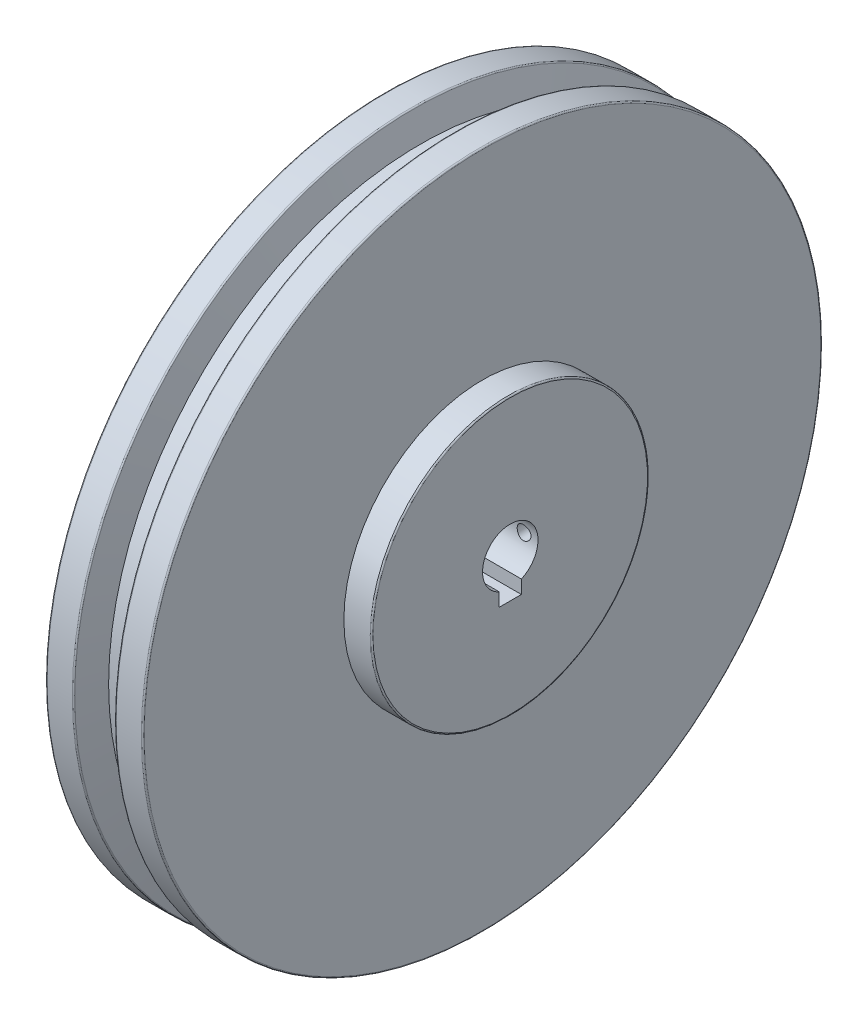
SolidWorks part; units mm, degrees
ref_plane "Front Plane" through (0, 0, 0) normal (0, 0, 1) x (1, 0, 0)
ref_plane "Top Plane" through (0, 0, 0) normal (0, 1, 0) x (1, 0, 0)
ref_plane "Right Plane" through (0, 0, 0) normal (1, 0, 0) x (0, 0, -1)
sketch "Sketch1" plane through (0, 0, 0) normal (0, 0, 1) x (1, 0, 0)
  line L0 (0, 0) -> (43.9763, 0) construction
  line L1 (0, -20) -> (0, -122)
  line L2 (0.5, -122.5) -> (9.6163, -122.5)
  line L3 (10.0993, -122.1294) -> (12.6795, -112.5)
  line L4 (12.6795, -112.5) -> (22.3205, -112.5)
  line L5 (22.3205, -112.5) -> (24.9007, -122.1294)
  line L6 (25.3837, -122.5) -> (34.5, -122.5)
  line L7 (35, -122) -> (35, -50)
  line L8 (35, -50) -> (44.5, -50)
  line L9 (45, -49.5) -> (45, -10)
  line L10 (45, -10) -> (2.5, -10)
  line L11 (0, -20) -> (2.5, -10)
  arc A0 (44.5, -50) -> (45, -49.5) centre (44.5, -49.5) ccw
  arc A1 (34.5, -122.5) -> (35, -122) centre (34.5, -122) ccw
  arc A2 (24.9007, -122.1294) -> (25.3837, -122.5) centre (25.3837, -122) ccw
  arc A3 (9.6163, -122.5) -> (10.0993, -122.1294) centre (9.6163, -122) ccw
  arc A4 (0, -122) -> (0.5, -122.5) centre (0.5, -122) ccw
  point P18 (35, -122.5)
  point P21 (25, -122.5)
  point P24 (10, -122.5)
  point P27 (0, -122.5)
  dimension "D14" = 100
  dimension "D15" = 0.5
  dimension "D10" = 0.5
  dimension "D1" = 20
  dimension "D2" = 245
  dimension "D3" = 225
  dimension "D4" = 245
  dimension "D5" = 105
  dimension "D6" = 10
  dimension "D7" = 10
  dimension "D8" = 15
  dimension "D9" = 105
  dimension "D11" = 45
  dimension "D12" = 2.5
  dimension "D13" = 10
revolve "Revolve1" add sketch "Sketch1" angle 360 about L0
sketch "Esboço1" plane through (0, 0, 0) normal (-1, 0, 0) x (0, 0, 1)
  line L0 (0, 0) -> (0, -10) construction
  line L1 (4, -14) -> (-4, -14)
  line L2 (4, -14) -> (4, -6)
  line L3 (4, -6) -> (-4, -6)
  line L4 (-4, -14) -> (-4, -6)
  line L5 (4, -14) -> (-4, -6) construction
  line L6 (4, -6) -> (-4, -14) construction
  circle A0 centre (0, 0) radius 10 construction
  point P0 (0, -10)
  dimension "D1" = 8
  dimension "D2" = 8
extrude "Corte-extrusão1" cut sketch "Esboço1" against normal through all
sketch "Esboço3" plane through (0, 0, 0) normal (0, 0, 1) x (1, 0, 0)
  line L0 (45, 0) -> (35, 0) construction
  line L1 (45, -49.5) -> (45, 49.5) construction
  line L2 (35, -50) -> (35, 50) construction
  circle A0 centre (40, 0) radius 2.5
  dimension "D1" = 5
extrude "Corte-extrusão2" cut sketch "Esboço3" against normal through all
cosmetic thread "Representação de rosca1" parameters "D1"=5, "D2"=6
